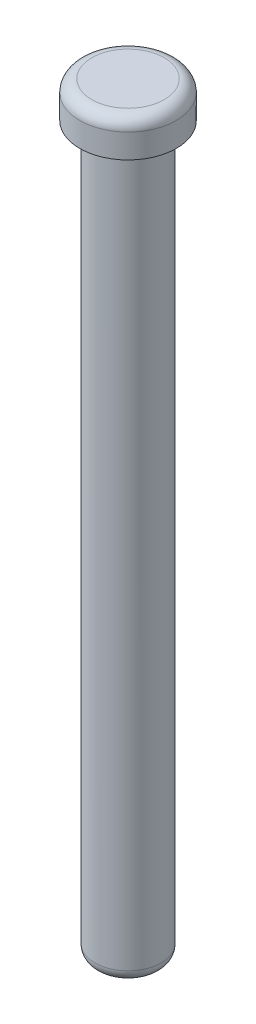
SolidWorks part; units mm, degrees
ref_plane "Front Plane" through (0, 0, 0) normal (0, 0, 1) x (1, 0, 0)
ref_plane "Top Plane" through (0, 0, 0) normal (0, 1, 0) x (1, 0, 0)
ref_plane "Right Plane" through (0, 0, 0) normal (1, 0, 0) x (0, 0, -1)
sketch "Sketch1" plane through (0, 0, 0) normal (0, 0, 1) x (1, 0, 0)
  line L0 (0, 0) -> (0, 63)
  line L1 (0, 63) -> (-4, 63)
  line L2 (-4, 63) -> (-4, 60)
  line L3 (-4, 60) -> (-2.75, 60)
  line L4 (-2.75, 60) -> (-2.75, 0)
  line L5 (-2.75, 0) -> (0, 0)
  dimension "D1" = 4
  dimension "D2" = 2.75
  dimension "D3" = 3
  dimension "D4" = 60
revolve "Revolve1" add sketch "Sketch1" angle 360 about L0
fillet "Fillet1" radius 1 2 edges at (0, 0, -2.75) (0, 63, -4)
